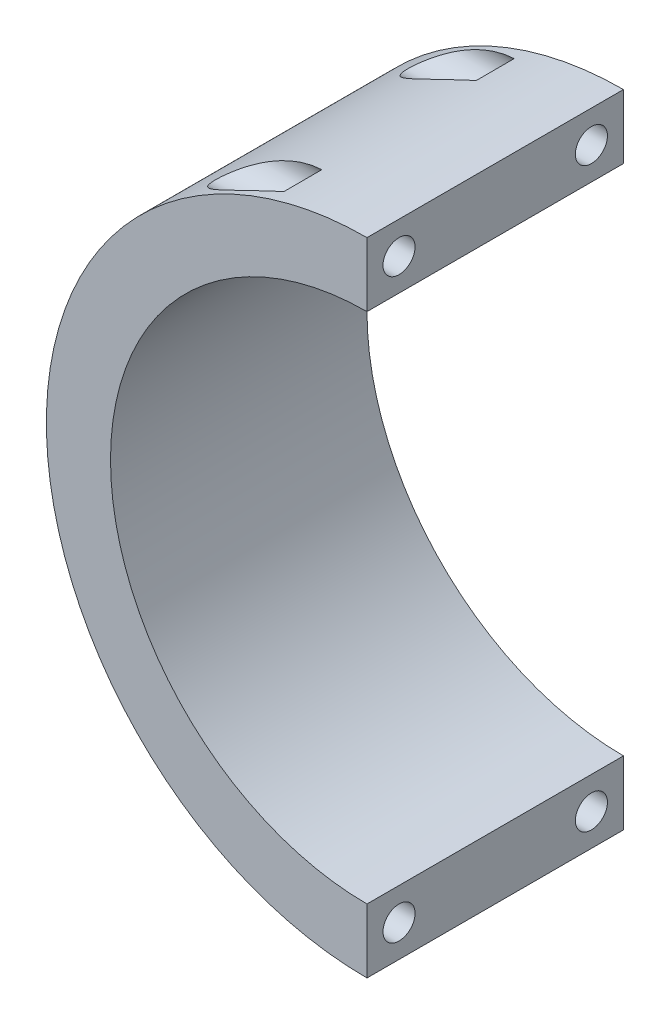
SolidWorks part; units mm, degrees
ref_plane "Front Plane" through (0, 0, 0) normal (0, 0, 1) x (1, 0, 0)
ref_plane "Top Plane" through (0, 0, 0) normal (0, 1, 0) x (1, 0, 0)
ref_plane "Right Plane" through (0, 0, 0) normal (1, 0, 0) x (0, 0, -1)
sketch "Sketch1" plane through (0, 0, 0) normal (0, 0, 1) x (1, 0, 0)
  line L1 (0, 101.6) -> (0, 114.3)
  line L2 (0, 0) -> (0, -12.7)
  arc A0 (0, 101.6) -> (0, 0) centre (0, 50.8) ccw
  arc A1 (0, 114.3) -> (0, -12.7) centre (0, 50.8) ccw
  dimension "D1" = 101.6
  dimension "D2" = 12.7
  dimension "D3" = 12.7
extrude "Boss-Extrude1" add sketch "Sketch1" along normal blind 50.8
sketch "Sketch2" plane through (0, 0, 0) normal (1, 0, 0) x (0, 0, -1)
  line L0 (-44.45, 114.3) -> (-44.45, 107.95) construction
  line L1 (-50.8, 114.3) -> (0, 114.3) construction
  line L2 (-44.45, 107.95) -> (-50.8, 107.95) construction
  line L3 (-50.8, 101.6) -> (-50.8, 114.3) construction
  line L4 (0, 114.3) -> (-6.35, 114.3)
  line L5 (-6.35, 114.3) -> (-6.35, 107.95)
  line L6 (0, 50.8) -> (32.0085, 50.8)
  line L7 (0, 0) -> (0, 101.6) construction
  circle A0 centre (-44.45, 107.95) radius 3.175
  circle A1 centre (-6.35, 107.95) radius 3.175
  circle A2 centre (-6.35, -6.35) radius 3.175
  circle A3 centre (-44.45, -6.35) radius 3.175
  dimension "D3" = 6.35
  dimension "D7" = 6.35
  dimension "D1" = 6.35
  dimension "D2" = 6.35
  dimension "D5" = 6.35
  dimension "D6" = 6.35
extrude "Cut-Extrude1" cut sketch "Sketch2" against normal through all
ref_plane "Plane1" through (-38.1, 0, 0) normal (1, 0, 0) x (0, 0, -1)
sketch "Sketch3" plane through (-38.1, 0, 0) normal (1, 0, 0) x (0, 0, -1)
  circle A0 centre (-44.45, 107.95) radius 5.08
  circle A1 centre (-6.35, 107.95) radius 5.08
  circle A2 centre (-6.35, -6.35) radius 5.08
  circle A3 centre (-44.45, -6.35) radius 5.08
  dimension "D1" = 10.16
  dimension "D2" = 10.16
  dimension "D3" = 10.16
  dimension "D4" = 10.16
extrude "Cut-Extrude2" cut sketch "Sketch3" along normal blind 19.05 contours A0 | A1 | A3 | A2
